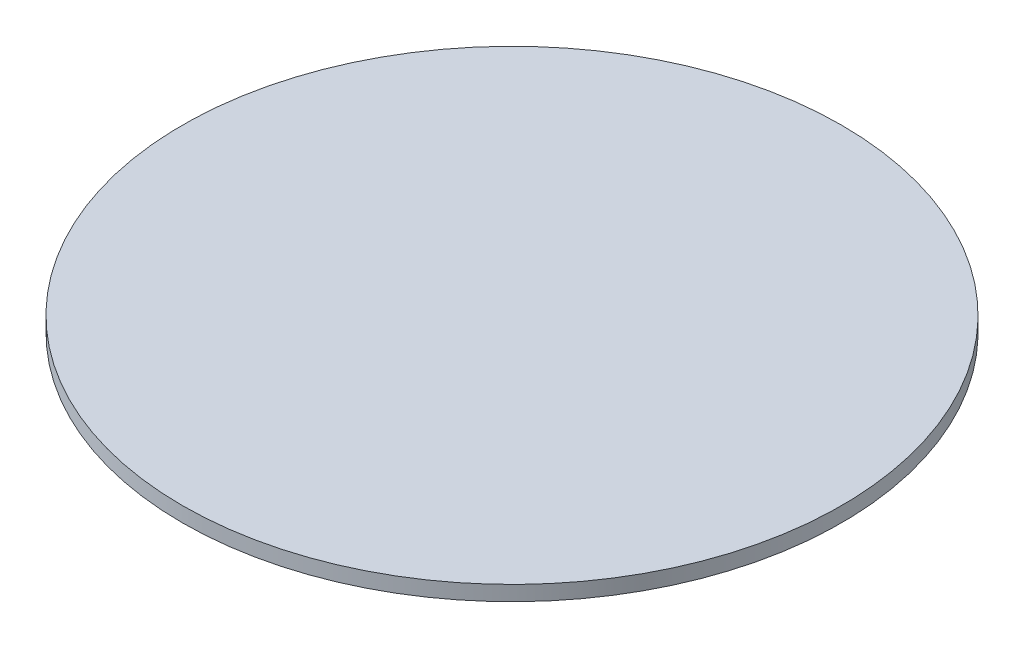
SolidWorks part; units mm, degrees
ref_plane "Plan de face" through (0, 0, 0) normal (0, 0, 1) x (1, 0, 0)
ref_plane "Plan de dessus" through (0, 0, 0) normal (0, 1, 0) x (1, 0, 0)
ref_plane "Plan de droite" through (0, 0, 0) normal (1, 0, 0) x (0, 0, -1)
sketch "Esquisse1" plane through (0, 0, 0) normal (0, 1, 0) x (1, 0, 0)
  circle A0 centre (0, 0) radius 17.62
extrude "Boss.-Extru.1" add sketch "Esquisse1" along normal blind 0.8
